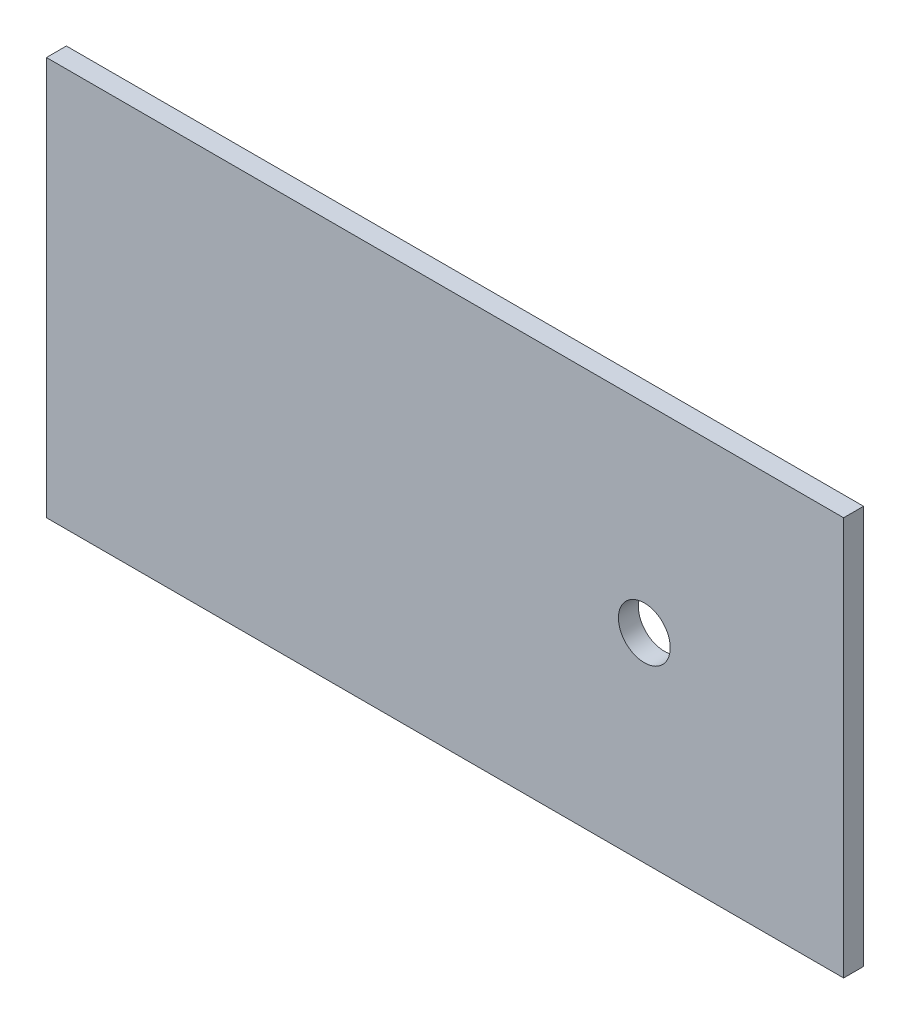
SolidWorks part; units mm, degrees
ref_plane "Front Plane" through (0, 0, 0) normal (0, 0, 1) x (1, 0, 0)
ref_plane "Top Plane" through (0, 0, 0) normal (0, 1, 0) x (1, 0, 0)
ref_plane "Right Plane" through (0, 0, 0) normal (1, 0, 0) x (0, 0, -1)
sketch "Sketch1" plane through (0, 0, 0) normal (0, 0, 1) x (1, 0, 0)
  line L1 (-100, 50) -> (100, 50)
  line L2 (-100, 50) -> (-100, -50)
  line L3 (-100, -50) -> (100, -50)
  line L4 (100, 50) -> (100, -50)
  line L5 (-100, 50) -> (100, -50) construction
  line L6 (-100, -50) -> (100, 50) construction
  point P0 (0, 0)
  dimension "D1" = 200
  dimension "D2" = 100
extrude "Boss-Extrude1" add sketch "Sketch1" along normal blind 5 contours L1 L4 L3 L2
sketch "Sketch2" plane through (0, 0, 5) normal (0, 0, 1) x (1, 0, 0)
  circle A0 centre (50, 0) radius 6.5
extrude "Cut-Extrude1" cut sketch "Sketch2" against normal blind 5
